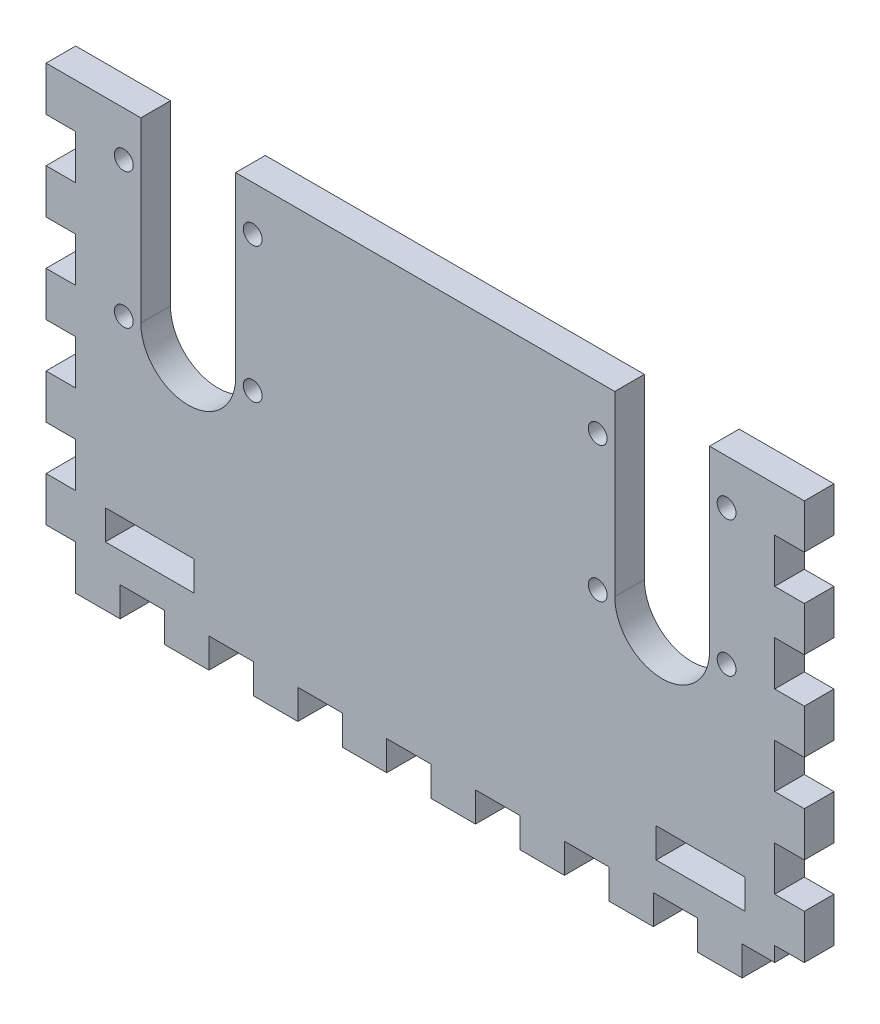
SolidWorks part; units mm, degrees
material "Pine"
ref_plane "Front Plane" through (0, 0, 0) normal (0, 0, 1) x (1, 0, 0)
ref_plane "Top Plane" through (0, 0, 0) normal (0, 1, 0) x (1, 0, 0)
ref_plane "Right Plane" through (0, 0, 0) normal (1, 0, 0) x (0, 0, -1)
sketch "Sketch1" plane through (0, 0, 0) normal (0, 0, 1) x (1, 0, 0)
  line L0 (124.46, -76.2) -> (143.51, -76.2)
  line L1 (0, 0) -> (149.86, 0)
  line L2 (0, 0) -> (0, -88.9)
  line L3 (0, -88.9) -> (149.86, -88.9)
  line L4 (149.86, 0) -> (149.86, -88.9)
  line L5 (6.35, -76.2) -> (25.4, -76.2)
  line L6 (6.35, -76.2) -> (6.35, -82.55)
  line L7 (6.35, -82.55) -> (25.4, -82.55)
  line L8 (25.4, -76.2) -> (25.4, -82.55)
  line L9 (124.46, -76.2) -> (124.46, -82.55)
  line L10 (124.46, -82.55) -> (143.51, -82.55)
  line L11 (143.51, -76.2) -> (143.51, -82.55)
  point P9 (6.35, -79.375)
  dimension "D1" = 149.86
  dimension "D2" = 88.9
  dimension "D3" = 19.05
  dimension "D4" = 6.35
  dimension "D5" = 6.35
  dimension "D6" = 6.35
  dimension "D7" = 19.05
  dimension "D8" = 6.35
  dimension "D9" = 6.35
  dimension "D10" = 6.35
extrude "General Shape" add sketch "Sketch1" along normal blind 6.35
sketch "Sketch4" plane through (0, 0, 6.35) normal (0, 0, 1) x (1, 0, 0)
  line L0 (24.13, 0) -> (24.13, -38.1) construction
  line L1 (149.86, 0) -> (0, 0) construction
  line L2 (34.29, 0) -> (34.29, -38.1)
  line L3 (13.97, 0) -> (13.97, -38.1)
  line L4 (125.73, 0) -> (125.73, -38.1) construction
  line L7 (13.97, -38.1) -> (0, -38.1) construction
  line L8 (0, 0) -> (0, -88.9) construction
  line L9 (135.89, 0) -> (135.89, -38.1)
  line L10 (135.89, -38.1) -> (149.86, -38.1) construction
  line L11 (115.57, 0) -> (115.57, -38.1)
  line L12 (24.13, -38.1) -> (24.13, -88.9) construction
  line L13 (0, -88.9) -> (149.86, -88.9) construction
  line L14 (149.86, -88.9) -> (149.86, 0) construction
  arc A0 (34.29, 0) -> (13.97, 0) centre (24.13, 0) ccw
  arc A1 (13.97, -38.1) -> (34.29, -38.1) centre (24.13, -38.1) ccw
  circle A4 centre (37.9476, -9.6266) radius 2.0193
  circle A5 centre (37.9476, -38.6588) radius 2.0193
  circle A6 centre (10.3124, -38.6588) radius 2.0193
  circle A7 centre (10.3124, -9.6266) radius 2.0193
  circle A8 centre (139.5476, -9.6266) radius 2.0193
  circle A9 centre (111.9124, -9.6266) radius 2.0193
  circle A10 centre (111.9124, -38.6588) radius 2.0193
  circle A11 centre (139.5476, -38.6588) radius 2.0193
  arc A12 (135.89, 0) -> (115.57, 0) centre (125.73, 0) ccw
  arc A13 (115.57, -38.1) -> (135.89, -38.1) centre (125.73, -38.1) ccw
  point P4 (24.13, -19.05)
  point P9 (24.13, -48.26)
  point P14 (125.73, -19.05)
  dimension "D2" = 10.16
  dimension "D5" = 13.8176
  dimension "D6" = 4.0386
  dimension "D7" = 9.6266
  dimension "D9" = 2
  dimension "D1" = 48.26
  dimension "D3" = 2
  dimension "D4" = 101.6
  dimension "D10" = 29.0322
extrude "Slot Cut-Outs" cut sketch "Sketch4" against normal up to surface (6.35 mm away) up to face at (15.875, -79.375, 0)
sketch "Sketch5" plane through (0, 0, 6.35) normal (0, 0, 1) x (1, 0, 0)
  line L1 (0, 0) -> (-6.35, 0)
  line L2 (0, 0) -> (0, -9.525)
  line L3 (0, -9.525) -> (-6.35, -9.525)
  line L4 (-6.35, 0) -> (-6.35, -9.525)
  line L28 (0, -19.05) -> (0, -28.575)
  line L29 (0, -19.05) -> (-6.35, -19.05)
  line L30 (-6.35, -19.05) -> (-6.35, -28.575)
  line L31 (0, -28.575) -> (-6.35, -28.575)
  line L32 (0, -38.1) -> (0, -47.625)
  line L33 (0, -38.1) -> (-6.35, -38.1)
  line L34 (-6.35, -38.1) -> (-6.35, -47.625)
  line L35 (0, -47.625) -> (-6.35, -47.625)
  line L36 (0, -57.15) -> (0, -66.675)
  line L37 (0, -57.15) -> (-6.35, -57.15)
  line L38 (-6.35, -57.15) -> (-6.35, -66.675)
  line L39 (0, -66.675) -> (-6.35, -66.675)
  line L40 (0, -76.2) -> (0, -85.725)
  line L41 (0, -76.2) -> (-6.35, -76.2)
  line L42 (-6.35, -76.2) -> (-6.35, -85.725)
  line L43 (0, -85.725) -> (-6.35, -85.725)
  line L44 (74.93, 0) -> (74.93, -88.9) construction
  line L45 (115.57, 0) -> (34.29, 0) construction
  line L46 (0, -88.9) -> (149.86, -88.9) construction
  line L47 (149.86, -76.2) -> (156.21, -76.2)
  line L48 (156.21, -76.2) -> (156.21, -85.725)
  line L49 (149.86, -85.725) -> (156.21, -85.725)
  line L50 (149.86, -76.2) -> (149.86, -85.725)
  line L51 (149.86, -57.15) -> (156.21, -57.15)
  line L52 (156.21, -57.15) -> (156.21, -66.675)
  line L53 (149.86, -66.675) -> (156.21, -66.675)
  line L54 (149.86, -57.15) -> (149.86, -66.675)
  line L55 (149.86, -38.1) -> (156.21, -38.1)
  line L56 (156.21, -38.1) -> (156.21, -47.625)
  line L57 (149.86, -47.625) -> (156.21, -47.625)
  line L58 (149.86, -38.1) -> (149.86, -47.625)
  line L59 (149.86, -19.05) -> (156.21, -19.05)
  line L60 (156.21, -19.05) -> (156.21, -28.575)
  line L61 (149.86, -28.575) -> (156.21, -28.575)
  line L62 (149.86, -19.05) -> (149.86, -28.575)
  line L63 (149.86, -9.525) -> (156.21, -9.525)
  line L64 (156.21, 0) -> (156.21, -9.525)
  line L65 (149.86, 0) -> (156.21, 0)
  line L66 (149.86, 0) -> (149.86, -9.525)
  line L67 (28.575, -88.9) -> (28.575, -95.25)
  line L68 (0, -88.9) -> (9.525, -88.9)
  line L69 (0, -88.9) -> (0, -95.25)
  line L70 (0, -95.25) -> (9.525, -95.25)
  line L71 (9.525, -88.9) -> (9.525, -95.25)
  line L72 (19.05, -88.9) -> (19.05, -95.25)
  line L73 (19.05, -88.9) -> (28.575, -88.9)
  line L74 (19.05, -95.25) -> (28.575, -95.25)
  line L75 (47.625, -88.9) -> (47.625, -95.25)
  line L76 (38.1, -88.9) -> (38.1, -95.25)
  line L77 (38.1, -88.9) -> (47.625, -88.9)
  line L78 (38.1, -95.25) -> (47.625, -95.25)
  line L79 (66.675, -88.9) -> (66.675, -95.25)
  line L80 (57.15, -88.9) -> (57.15, -95.25)
  line L81 (57.15, -88.9) -> (66.675, -88.9)
  line L82 (57.15, -95.25) -> (66.675, -95.25)
  line L83 (85.725, -88.9) -> (85.725, -95.25)
  line L84 (76.2, -88.9) -> (76.2, -95.25)
  line L85 (76.2, -88.9) -> (85.725, -88.9)
  line L86 (76.2, -95.25) -> (85.725, -95.25)
  line L87 (104.775, -88.9) -> (104.775, -95.25)
  line L88 (95.25, -88.9) -> (95.25, -95.25)
  line L89 (95.25, -88.9) -> (104.775, -88.9)
  line L90 (95.25, -95.25) -> (104.775, -95.25)
  line L91 (123.825, -88.9) -> (123.825, -95.25)
  line L92 (114.3, -88.9) -> (114.3, -95.25)
  line L93 (114.3, -88.9) -> (123.825, -88.9)
  line L94 (114.3, -95.25) -> (123.825, -95.25)
  line L95 (142.875, -88.9) -> (142.875, -95.25)
  line L96 (133.35, -88.9) -> (133.35, -95.25)
  line L97 (133.35, -88.9) -> (142.875, -88.9)
  line L98 (133.35, -95.25) -> (142.875, -95.25)
  dimension "D1" = 6.35
  dimension "D2" = 9.525
  dimension "D4" = 6.35
  dimension "D5" = 9.525
  dimension "D7" = 9.525
  dimension "D8" = 9.525
  dimension "D3" = 5
  dimension "D6" = 8
extrude "Edge Teeth" add sketch "Sketch5" against normal up to surface (6.35 mm away) up to face at (113.9317, -38.6588, 0)
